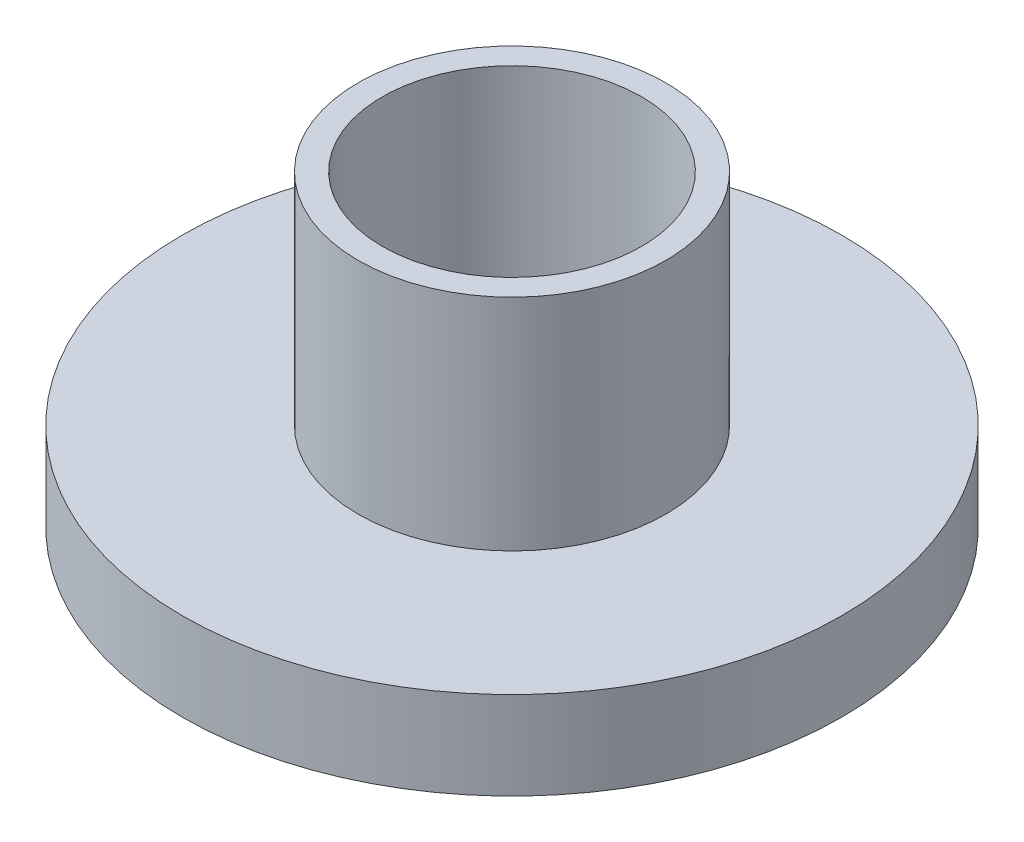
SolidWorks part; units mm, degrees
ref_plane "Front Plane" through (0, 0, 0) normal (0, 0, 1) x (1, 0, 0)
ref_plane "Top Plane" through (0, 0, 0) normal (0, 1, 0) x (1, 0, 0)
ref_plane "Right Plane" through (0, 0, 0) normal (1, 0, 0) x (0, 0, -1)
sketch "Sketch9" plane through (0, 0, 0) normal (0, 1, 0) x (1, 0, 0)
  circle A0 centre (0, 0) radius 7.5
  dimension "D1" = 15
extrude "Boss-Extrude4" add sketch "Sketch9" along normal blind 2
sketch "Sketch10" plane through (0, 2, 0) normal (0, 1, 0) x (1, 0, 0)
  circle A0 centre (0, 0) radius 3.5
  dimension "D1" = 7
extrude "Boss-Extrude5" add sketch "Sketch10" along normal blind 5
sketch "Sketch11" plane through (0, 7, 0) normal (0, 1, 0) x (1, 0, 0)
  circle A0 centre (0, 0) radius 2.95
  dimension "D1" = 5.9
extrude "Cut-Extrude3" cut sketch "Sketch11" against normal blind 14
